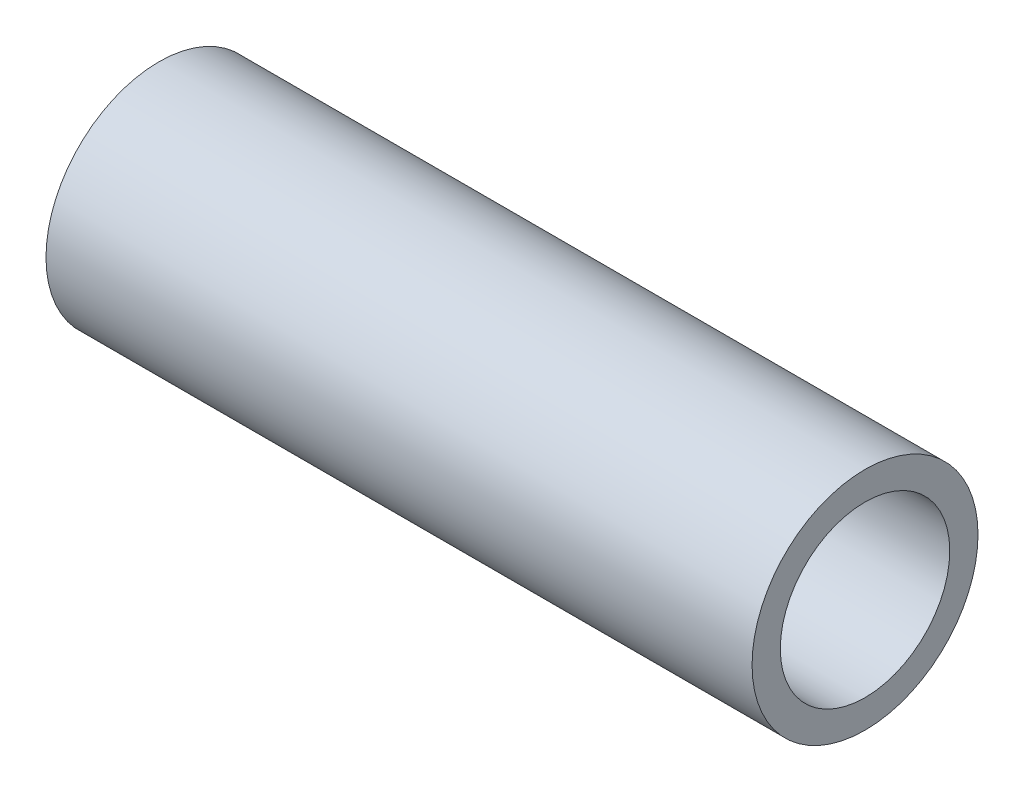
SolidWorks part; units mm, degrees
ref_plane "Front Plane" through (0, 0, 0) normal (0, 0, 1) x (1, 0, 0)
ref_plane "Top Plane" through (0, 0, 0) normal (0, 1, 0) x (1, 0, 0)
ref_plane "Right Plane" through (0, 0, 0) normal (1, 0, 0) x (0, 0, -1)
sketch "Sketch1" plane through (0, 0, 0) normal (1, 0, 0) x (0, 0, -1)
  circle A0 centre (0, 0) radius 1.5
  circle A1 centre (0, 0) radius 2
  dimension "D1" = 3
  dimension "D2" = 4
extrude "Boss-Extrude1" add sketch "Sketch1" along normal blind 12.5
